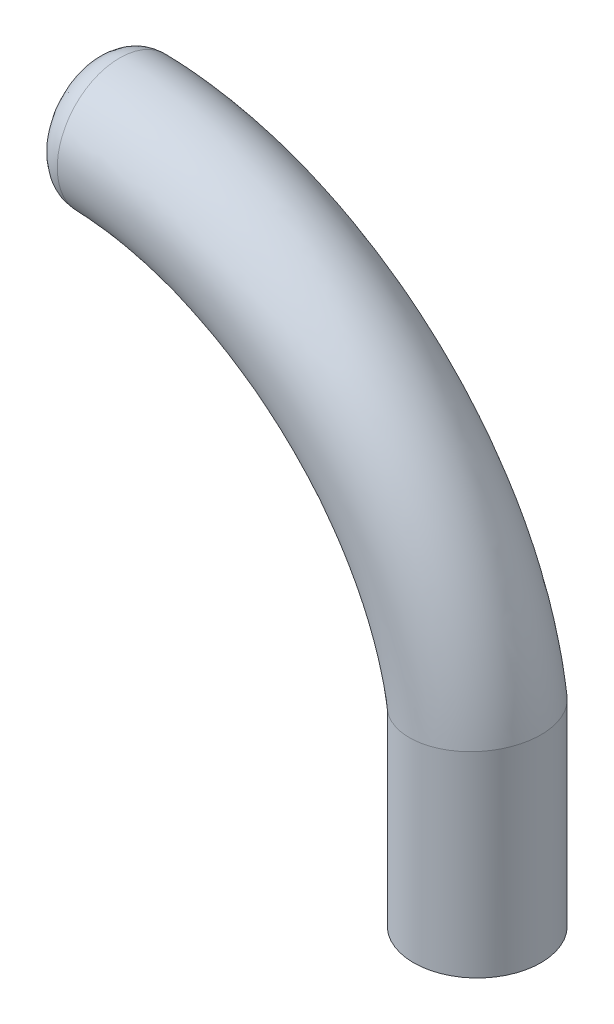
SolidWorks part; units mm, degrees
ref_plane "Front Plane" through (0, 0, 0) normal (0, 0, 1) x (1, 0, 0)
ref_plane "Top Plane" through (0, 0, 0) normal (0, 1, 0) x (1, 0, 0)
ref_plane "Right Plane" through (0, 0, 0) normal (1, 0, 0) x (0, 0, -1)
sketch "Sketch1" plane through (0, 0, 0) normal (0, 1, 0) x (1, 0, 0)
  circle A0 centre (0, 0) radius 5
  dimension "D1" = 10
sketch "Sketch2" plane through (0, 0, 0) normal (0, 0, 1) x (1, 0, 0)
  line L0 (0, 0) -> (0, 40) construction
  line L1 (0, 40) -> (-30, 40) construction
  line L2 (0, 15.1665) -> (0, 0)
  spline S0 degree 3 poles (-30, 40) (-15.6793, 40.6982) (-1.9508, 29.1682) (0, 15.1665) knots 0 0 0 0 1 1 1 1
  dimension "D1" = 40
  dimension "D2" = 30
sweep "Sweep1" add profiles "Sketch1" path "Sketch2"
fillet "Fillet1" radius 2 1 edges at (-30, 40, 5)
